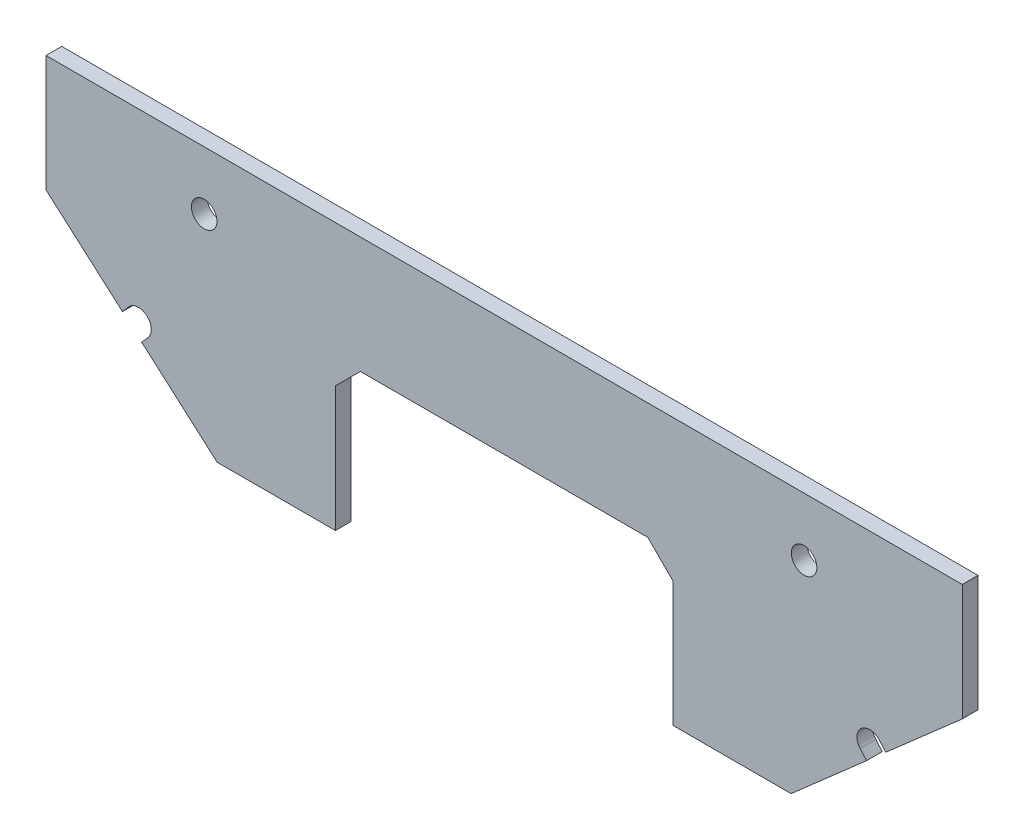
SolidWorks part; units mm, degrees
ref_plane "Front Plane" through (0, 0, 0) normal (0, 0, 1) x (1, 0, 0)
ref_plane "Top Plane" through (0, 0, 0) normal (0, 1, 0) x (1, 0, 0)
ref_plane "Right Plane" through (0, 0, 0) normal (1, 0, 0) x (0, 0, -1)
sketch "Sketch1" plane through (0, 0, 1.63) normal (0, 0, 1) x (1, 0, 0)
  line L1 (5.9182, -5.9182) -> (-87.1982, -5.9182)
  line L2 (5.9182, -5.9182) -> (5.9182, 5.9182)
  line L3 (5.9182, 5.9182) -> (-87.1982, 5.9182)
  line L4 (-87.1982, -5.9182) -> (-87.1982, 5.9182)
  line L5 (5.9182, -5.9182) -> (-87.1982, 5.9182) construction
  line L6 (5.9182, 5.9182) -> (-87.1982, -5.9182) construction
  line L7 (-4.3624, -5.9182) -> (4.3624, -5.9182) construction
  line L8 (5.9182, -4.3625) -> (5.9182, 4.3625) construction
  line L9 (4.3624, 5.9182) -> (-4.3624, 5.9182) construction
  line L10 (-87.1982, 4.3624) -> (-87.1982, -4.3624) construction
  point P4 (-40.64, 0)
extrude "Boss-Extrude1" add sketch "Sketch1" along normal blind 1.6002
sketch "Sketch4" plane through (0, 0, 1.63) normal (0, 0, -1) x (-1, 0, 0)
  line L0 (87.1982, -5.9182) -> (69.8038, -21.1895)
  line L1 (69.8038, -21.1895) -> (57.785, -21.1895)
  line L2 (57.785, -21.1895) -> (57.785, -5.9182)
  line L3 (87.1982, -5.9182) -> (-5.9182, -5.9182) construction
  line L4 (87.1982, -5.9182) -> (57.785, -5.9182)
  line L6 (121.532, 19.2031) -> (72.6264, -23.7332) construction
  line L8 (57.785, -22.4595) -> (70.7114, -22.4595) construction
  line L9 (56.515, -10.7755) -> (56.515, -18.3955) construction
  line L10 (40.64, -5.9182) -> (40.64, 5.9182) construction
  line L11 (87.1982, -5.9182) -> (-5.9182, -5.9182) construction
  line L12 (-5.9182, 5.9182) -> (87.1982, 5.9182) construction
  line L13 (-5.9182, -5.9182) -> (23.495, -5.9182)
  line L14 (23.495, -21.1895) -> (23.495, -5.9182)
  line L15 (11.4762, -21.1895) -> (23.495, -21.1895)
  line L16 (-5.9182, -5.9182) -> (11.4762, -21.1895)
  dimension "D1" = 1.27
  dimension "D2" = 1.27
extrude "Boss-Extrude2" add sketch "Sketch4" against normal through all
chamfer "Chamfer1" distance 2.54 angle 45 2 edges at (-23.495, -5.9182, 2.4301)
hole_wizard "Ø2.6 (2.6) Diameter Hole1" positions "Sketch3" profile "Sketch2" hole size "Ø2.6" standard "ANSI Metric" end condition through all
sketch "Sketch3" plane through (0, 0, 3.2302) normal (0, 0, 1) x (1, 0, 0)
  line L0 (-87.1982, 0) -> (5.9182, 0) construction
  line L3 (-87.1982, 5.9182) -> (-87.1982, -5.9182) construction
  line L7 (5.9182, -5.9182) -> (5.9182, 5.9182) construction
  point P32 (-10.16, 0)
  point P35 (-71.12, 0)
  point P39 (-77.7983, -12.8551)
  point P42 (-3.4817, -12.8551)
sketch "Sketch2" plane through (-10.16, 0, 3.2302) normal (1, 0, 0) x (0, -1, 0)
  line L0 (0, 0) -> (0, 1.6002)
  line L1 (0, 1.6002) -> (1.3, 1.6002)
  line L2 (1.3, 1.6002) -> (1.3, 0)
  line L5 (1.3, 0) -> (0, 0)
  line L11 (0, -6.35) -> (0, 107.95) construction
  dimension "Thru Hole Dia." = 2.6
  dimension "Thru Hole Depth" = 1.6002
sketch "Sketch6" plane through (0, 0, 1.63) normal (0, 0, -1) x (-1, 0, 0)
  line L0 (79.4275, -12.7404) -> (78.7752, -11.9974)
  line L1 (79.0849, -13.0412) -> (87.1982, -5.9182) construction
  line L2 (78.7752, -11.9974) -> (76.8214, -13.7128)
  line L3 (76.8214, -13.7128) -> (77.4737, -14.4557)
  line L4 (69.8038, -21.1895) -> (77.8163, -14.155) construction
  line L5 (79.4275, -12.7404) -> (77.4737, -14.4557)
  line L6 (40.64, 5.9182) -> (40.64, -5.8225) construction
  line L7 (-5.9182, 5.9182) -> (87.1982, 5.9182) construction
  line L9 (1.8525, -12.7404) -> (3.8063, -14.4557)
  line L10 (4.4586, -13.7128) -> (3.8063, -14.4557)
  line L11 (2.5048, -11.9974) -> (4.4586, -13.7128)
  line L12 (1.8525, -12.7404) -> (2.5048, -11.9974)
  arc A0 (79.0849, -13.0412) -> (77.8163, -14.155) centre (77.7983, -12.8551) ccw construction
extrude "Cut-Extrude1" cut sketch "Sketch6" against normal through all
sketch "EXTERNAL CONNECTOR ZONES" plane through (0, 0, 3.2302) normal (0, 0, 1) x (1, 0, 0)
  line L3 (-67.945, -21.1895) -> (-67.945, -8.3625)
  line L4 (-14.605, -7.0925) -> (-24.8607, -7.0925)
  line L5 (-13.335, -8.3625) -> (-13.335, -21.1895)
  line L6 (-24.8607, -7.0925) -> (-23.495, -8.4582)
  line L7 (-23.495, -21.1895) -> (-23.495, -8.4582)
  line L8 (-57.785, -8.4582) -> (-56.4193, -7.0925)
  line L9 (-57.785, -8.4582) -> (-57.785, -21.1895)
  line L10 (-57.785, -21.1895) -> (-67.945, -21.1895)
  line L11 (-56.4193, -7.0925) -> (-66.675, -7.0925)
  line L12 (-13.335, -21.1895) -> (-23.495, -21.1895)
  arc A2 (-66.675, -7.0925) -> (-67.945, -8.3625) centre (-66.675, -8.3625) ccw
  arc A3 (-13.335, -8.3625) -> (-14.605, -7.0925) centre (-14.605, -8.3625) ccw
sketch "REAR COMPONENT KEEP OUT ZONE" plane through (0, 0, 3.2302) normal (0, 0, 1) x (1, 0, 0)
  line L0 (-5.6911, -14.7948) -> (-4.3086, -16.3695) construction
  line L1 (0.1102, -12.4901) -> (-1.2723, -10.9154) construction
  line L2 (-76.9714, -16.3695) -> (-75.5889, -14.7948) construction
  line L3 (-80.0077, -10.9154) -> (-81.3902, -12.4901) construction
  line L4 (-5.6911, -14.7948) -> (-4.9998, -15.5822)
  line L5 (-0.581, -11.7027) -> (-1.2723, -10.9154)
  line L6 (-76.2802, -15.5822) -> (-75.5889, -14.7948)
  line L7 (-80.0077, -10.9154) -> (-80.699, -11.7027)
  line L8 (-76.2802, -15.5822) -> (-80.699, -11.7027)
  line L9 (-0.581, -11.7027) -> (-4.9998, -15.5822)
  arc A0 (-1.2723, -10.9154) -> (-5.6911, -14.7948) centre (-3.4817, -12.8551) ccw construction
  circle A1 centre (-10.16, 0) radius 2.3812 construction
  circle A2 centre (-30.48, 0) radius 2.3813 construction
  circle A3 centre (-50.8, 0) radius 2.3813 construction
  circle A4 centre (-71.12, 0) radius 2.3813 construction
  arc A5 (-75.5889, -14.7948) -> (-80.0077, -10.9154) centre (-77.7983, -12.8551) ccw construction
  arc A6 (-1.2723, -10.9154) -> (-5.6911, -14.7948) centre (-3.4817, -12.8551) ccw
  circle A7 centre (-10.16, 0) radius 2.3813
  circle A8 centre (-30.48, 0) radius 2.3813
  circle A9 centre (-50.8, 0) radius 2.3812
  circle A10 centre (-71.12, 0) radius 2.3813
  arc A11 (-75.5889, -14.7948) -> (-80.0077, -10.9154) centre (-77.7983, -12.8551) ccw
sketch "FRONT COMPONENT KEEP OUT ZONE" plane through (0, 0, 1.63) normal (0, 0, -1) x (-1, 0, 0)
  line L0 (0.581, -11.7027) -> (1.2723, -10.9154) construction
  line L1 (5.6911, -14.7948) -> (4.9998, -15.5822) construction
  line L2 (76.2802, -15.5822) -> (75.5889, -14.7948) construction
  line L3 (80.0077, -10.9154) -> (80.699, -11.7027) construction
  line L4 (0.581, -11.7027) -> (1.2723, -10.9154)
  line L5 (5.6911, -14.7948) -> (4.9998, -15.5822)
  line L6 (76.2802, -15.5822) -> (75.5889, -14.7948)
  line L7 (80.0077, -10.9154) -> (80.699, -11.7027)
  line L8 (0.581, -11.7027) -> (4.9998, -15.5822)
  line L9 (76.2802, -15.5822) -> (80.699, -11.7027)
  arc A0 (5.6911, -14.7948) -> (1.2723, -10.9154) centre (3.4817, -12.8551) ccw construction
  circle A1 centre (10.16, 0) radius 2.3812 construction
  circle A2 centre (71.12, 0) radius 2.3813 construction
  arc A3 (80.0077, -10.9154) -> (75.5889, -14.7948) centre (77.7983, -12.8551) ccw construction
  arc A4 (5.6911, -14.7948) -> (1.2723, -10.9154) centre (3.4817, -12.8551) ccw
  circle A5 centre (10.16, 0) radius 2.3813
  circle A6 centre (71.12, 0) radius 2.3813
  arc A7 (80.0077, -10.9154) -> (75.5889, -14.7948) centre (77.7983, -12.8551) ccw
